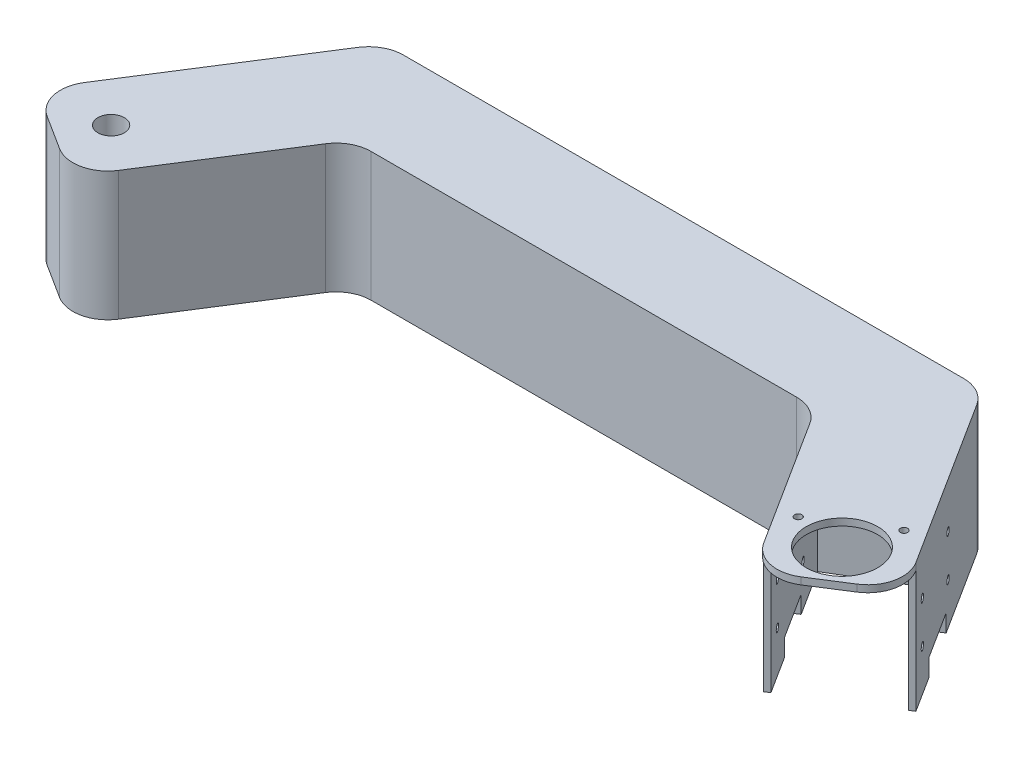
SolidWorks part; units mm, degrees
ref_plane "Front Plane" through (0, 0, 0) normal (0, 0, 1) x (1, 0, 0)
ref_plane "Top Plane" through (0, 0, 0) normal (0, 1, 0) x (1, 0, 0)
ref_plane "Right Plane" through (0, 0, 0) normal (1, 0, 0) x (0, 0, -1)
sketch "Sketch1" plane through (0, 0, 0) normal (0, 1, 0) x (1, 0, 0)
  line L4 (30.9136, -11.507) -> (61.4102, 36.4717)
  line L6 (80.7314, 7.8554) -> (57.6301, -28.4887)
  line L7 (43.8263, -31.5638) -> (33.9887, -25.3107)
  line L8 (89.1708, 12.4911) -> (211.3631, 12.4911)
  line L9 (69.8496, 41.1074) -> (230.6842, 41.1074)
  line L10 (150.2669, 12.4911) -> (150.2669, 90.3966) construction
  line L11 (256.7076, -31.5638) -> (266.5452, -25.3107)
  line L12 (219.8025, 7.8554) -> (242.9038, -28.4887)
  line L13 (269.6203, -11.507) -> (239.1237, 36.4717)
  arc A0 (69.8496, 41.1074) -> (61.4102, 36.4717) centre (69.8496, 31.1074) ccw
  arc A1 (89.1708, 12.4911) -> (80.7314, 7.8554) centre (89.1708, 2.4911) ccw
  arc A2 (43.8263, -31.5638) -> (57.6301, -28.4887) centre (49.1906, -23.1244) ccw
  arc A3 (30.9136, -11.507) -> (33.9887, -25.3107) centre (39.353, -16.8713) ccw
  arc A4 (269.6203, -11.507) -> (266.5452, -25.3107) centre (261.1808, -16.8713) cw
  arc A5 (256.7076, -31.5638) -> (242.9038, -28.4887) centre (251.3433, -23.1244) cw
  arc A6 (211.3631, 12.4911) -> (219.8025, 7.8554) centre (211.3631, 2.4911) cw
  arc A7 (230.6842, 41.1074) -> (239.1237, 36.4717) centre (230.6842, 31.1074) cw
  point P18 (150.2669, 41.1074)
  dimension "D1" = 10
  dimension "D2" = 10
  dimension "D3" = 10
extrude "Boss-Extrude1" add sketch "Sketch1" along normal blind 37
sketch "Sketch3" plane through (0, 37, 0) normal (0, 1, 0) x (1, 0, 0)
  line L1 (33.9887, -25.3107) -> (43.8263, -31.5638) construction
  line L2 (150.2669, 41.1074) -> (150.2669, -42.4536) construction
  line L3 (230.6842, 41.1074) -> (69.8496, 41.1074) construction
  line L4 (255.1892, -18.31) -> (261.6264, -28.4373) construction
  line L5 (256.7076, -31.5638) -> (266.5452, -25.3107) construction
  line L6 (45.3447, -18.31) -> (58.7029, -26.8008) construction
  line L7 (57.6301, -28.4887) -> (80.7314, 7.8554) construction
  line L8 (45.3447, -18.31) -> (31.9865, -9.8191) construction
  line L9 (61.4102, 36.4717) -> (30.9136, -11.507) construction
  line L10 (255.1892, -18.31) -> (268.5474, -9.8191) construction
  line L11 (269.6203, -11.507) -> (239.1237, 36.4717) construction
  circle A2 centre (255.1892, -18.31) radius 10.25
  circle A3 centre (259.9129, -5.2357) radius 1.05
  circle A4 centre (241.3461, -17.0372) radius 1.05
  circle A5 centre (45.3447, -18.31) radius 10.25 construction
  circle A6 centre (45.3447, -18.31) radius 3.7912
  dimension "D1" = 12
  dimension "D2" = 8.5
  dimension "D4" = 11
  dimension "D5" = 8.5
  dimension "D3" = 11
ref_plane "Plane1" through (150.265, 0, 0) normal (1, 0, 0) x (0, 0, -1)
extrude "Cut-Extrude1" cut sketch "Sketch3" against normal through all
sketch "Sketch9" plane through (0, 0, 0) normal (0, -1, 0) x (1, 0, 0)
  line L5 (220.7705, -9.1289) -> (250.1014, 37.0161)
  line L6 (219.8025, -7.8554) -> (242.9038, 28.4887) construction
  line L7 (250.1014, 37.0161) -> (274.286, 21.6436)
  line L8 (274.286, 21.6436) -> (245.3696, -23.8491)
  line L9 (245.3696, -23.8491) -> (220.7705, -9.1289)
  line L10 (269.6203, 11.507) -> (239.1237, -36.4717) construction
  line L11 (226.7399, 3.0589) -> (228.0059, 2.2542) construction
  line L12 (251.6247, -14.0082) -> (252.8906, -14.8129) construction
  line L13 (150.2669, -41.1074) -> (150.265, 31.662) construction
  line L16 (230.6842, -41.1074) -> (69.8496, -41.1074) construction
extrude "Cut-Extrude5" cut sketch "Sketch9" against normal blind 35
ref_plane "Plane3" through (81.7227, 0, 128.57) normal (0.5364, 0, 0.8439) x (0.8439, 0, -0.5364)
sketch "Sketch10" plane through (186.8247, 0, -118.7509) normal (0.8439, 0, -0.5364) x (-0.5364, 0, -0.8439)
  line L0 (-164.3445, 35) -> (-159.6123, 35) construction
  line L2 (-152.3445, 27.5727) -> (-152.3445, -27.5727) construction
  circle A0 centre (-148.3445, 24) radius 1.05
  circle A1 centre (-148.3445, 12) radius 1.05
  circle A2 centre (-124.3445, 12) radius 1.05
  circle A3 centre (-124.3445, 24) radius 1.05
  dimension "D1" = 2.1
  dimension "D2" = 24
  dimension "D3" = 24
  dimension "D4" = 12
  dimension "D5" = 11
  dimension "D6" = 4
extrude "Cut-Extrude6" cut sketch "Sketch10" against normal blind 35
ref_plane "Plane4" through (4.7592, 0, -7.4873) normal (-0.5364, 0, 0.8439) x (0.8439, 0, 0.5364)
sketch "Sketch15" plane through (160.1083, 0, -101.7692) normal (-0.8439, 0, 0.5364) x (0.5364, 0, 0.8439)
  line L0 (141.9114, 0) -> (141.9114, 5.0004)
  line L1 (111.2799, 0) -> (154.3445, 0) construction
  line L2 (141.9114, 5.0004) -> (126.1405, 5.0004)
  line L3 (126.1405, 5.0004) -> (126.1405, 0)
  line L4 (126.1405, 0) -> (141.9114, 0)
extrude "Cut-Extrude8" cut sketch "Sketch15" against normal blind 35
sketch "Sketch17" plane through (160.1083, 0, -101.7692) normal (-0.8439, 0, 0.5364) x (0.5364, 0, 0.8439)
  line L10 (154.3445, 37) -> (154.3445, 0) construction
  line L11 (164.78, 0) -> (154.3445, 0)
  line L12 (164.78, 0) -> (164.78, 35)
  line L13 (164.78, 35) -> (154.3445, 35)
  line L14 (154.3445, 0) -> (154.3445, 35)
extrude "Cut-Extrude10" cut sketch "Sketch17" against normal blind 38
